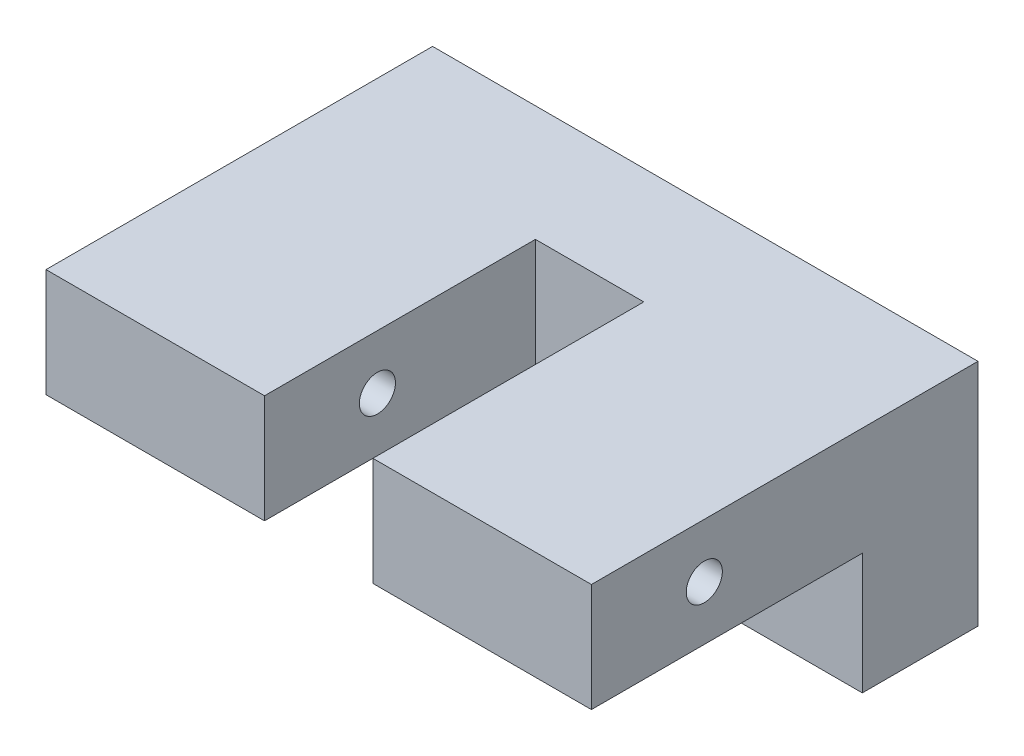
SolidWorks part; units mm, degrees
ref_plane "Front Plane" through (0, 0, 0) normal (0, 0, 1) x (1, 0, 0)
ref_plane "Top Plane" through (0, 0, 0) normal (0, 1, 0) x (1, 0, 0)
ref_plane "Right Plane" through (0, 0, 0) normal (1, 0, 0) x (0, 0, -1)
sketch "Sketch1" plane through (0, 0, 0) normal (0, 0, 1) x (1, 0, 0)
  line L1 (0, 0) -> (120.8, 0)
  line L2 (0, 0) -> (0, 50.8)
  line L3 (0, 50.8) -> (120.8, 50.8)
  line L4 (120.8, 0) -> (120.8, 50.8)
  dimension "D1" = 120.8
  dimension "D2" = 50.8
extrude "Boss-Extrude1" add sketch "Sketch1" along normal blind 85.62
sketch "Sketch2" plane through (0, 0, 85.62) normal (0, 0, 1) x (1, 0, 0)
  line L0 (120.8, 50.8) -> (0, 50.8) construction
  line L1 (48.4, 50.8) -> (72.4, 50.8)
  line L2 (48.4, 50.8) -> (48.4, 0)
  line L3 (48.4, 0) -> (72.4, 0)
  line L4 (72.4, 50.8) -> (72.4, 0)
  line L5 (0, 0) -> (120.8, 0) construction
  line L6 (0, 50.8) -> (48.4, 50.8) construction
  line L7 (72.4, 50.8) -> (120.8, 50.8) construction
  dimension "D1" = 24
extrude "Cut-Extrude1" cut sketch "Sketch2" against normal blind 60
sketch "Sketch3" plane through (120.8, 0, 0) normal (1, 0, 0) x (0, 1, 0)
  line L1 (50.8, 85.62) -> (38.8, 85.62) construction
  line L2 (50.8, 85.62) -> (50.8, 60.62) construction
  line L3 (50.8, 60.62) -> (38.8, 60.62) construction
  line L4 (38.8, 85.62) -> (38.8, 60.62) construction
  circle A0 centre (38.8, 60.62) radius 4
  dimension "D1" = 8
  dimension "D2" = 12
  dimension "D3" = 25
extrude "Cut-Extrude2" cut sketch "Sketch3" against normal through all
sketch "Sketch4" plane through (120.8, 0, 0) normal (1, 0, 0) x (0, 1, 0)
  line L0 (50.8, 85.62) -> (50.8, 0) construction
  line L1 (0, 85.62) -> (26.8, 85.62)
  line L2 (0, 85.62) -> (0, 25.62)
  line L3 (0, 25.62) -> (26.8, 25.62)
  line L4 (26.8, 85.62) -> (26.8, 25.62)
  dimension "D1" = 24
  dimension "D2" = 60
extrude "Cut-Extrude3" cut sketch "Sketch4" against normal through all
